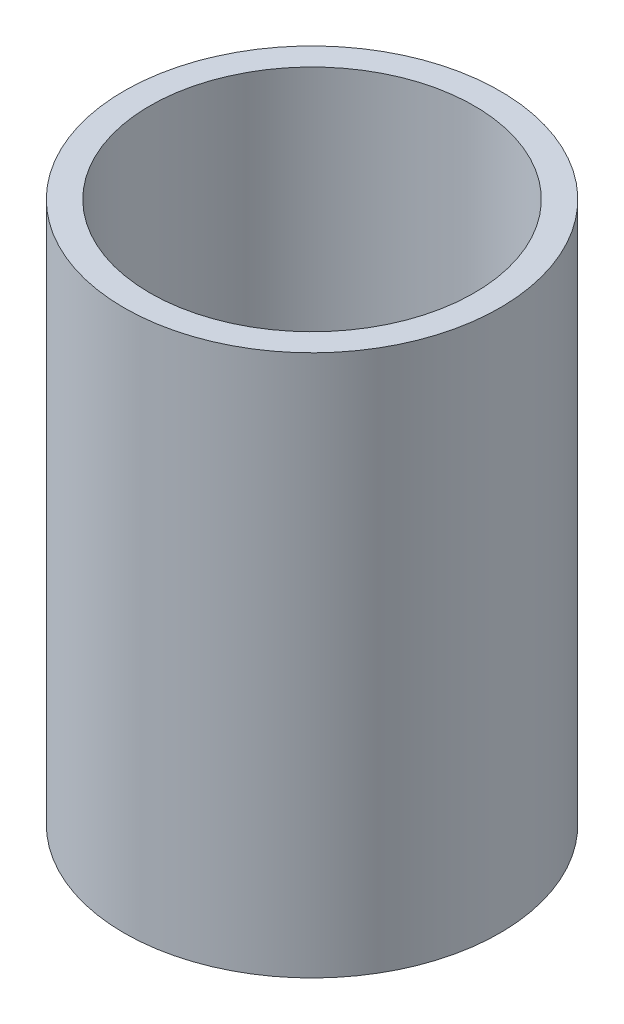
SolidWorks part; units mm, degrees
material "Corrugated Paper"
ref_plane "Front Plane" through (0, 0, 0) normal (0, 0, 1) x (1, 0, 0)
ref_plane "Top Plane" through (0, 0, 0) normal (0, 1, 0) x (1, 0, 0)
ref_plane "Right Plane" through (0, 0, 0) normal (1, 0, 0) x (0, 0, -1)
ref_axis "Axis1" through (0, 55, 0) along (0, -1, 0)
sketch "Sketch1" plane through (0, 0, 0) normal (0, 0, 1) x (1, 0, 0)
  line L1 (-46.2851, 45.6176) -> (-39.9351, 45.6176)
  line L2 (-46.2851, 45.6176) -> (-46.2851, -87.7324)
  line L3 (-46.2851, -87.7324) -> (-39.9351, -87.7324)
  line L4 (-39.9351, 45.6176) -> (-39.9351, -87.7324)
  line L5 (-38.1, 45.6176) -> (0, 45.6176) construction
  line L6 (-38.1, -87.7324) -> (0, -87.7324) construction
revolve "Revolve1" add sketch "Sketch1" angle 360 about axis through (0, 55, 0) along (0, -1, 0)
